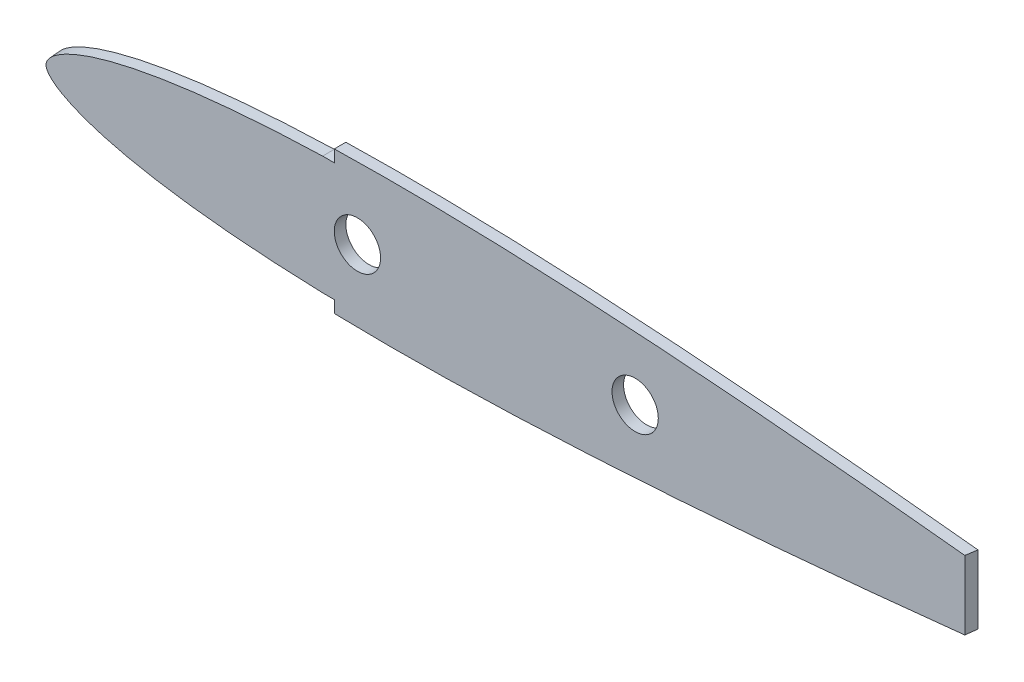
SolidWorks part; units mm, degrees
material "Balsa"
ref_plane "Front Plane" through (0, 0, 0) normal (0, 0, 1) x (1, 0, 0)
ref_plane "Top Plane" through (0, 0, 0) normal (0, 1, 0) x (1, 0, 0)
ref_plane "Right Plane" through (0, 0, 0) normal (1, 0, 0) x (0, 0, -1)
curve "Curve1"
  spline degree 3 poles (329.1277, -0.5559, 0) (329.1277, 0.5559, 0) (328.019, 0.4202, 0) (326.6142, 0.8156, 0) (324.0379, 1.0601, 0) (320.5673, 1.5846, 0) (316.0966, 2.17, 0) (310.7052, 2.8915, 0) (304.4072, 3.7071, 0) (297.2481, 4.6151, 0) (289.2699, 5.5996, 0) (280.5223, 6.6474, 0) (271.0592, 7.7455, 0) (260.9388, 8.8788, 0) (250.2237, 10.0335, 0) (238.9798, 11.1954, 0) (227.2766, 12.3494, 0) (215.1861, 13.4792, 0) (202.7829, 14.5702, 0) (190.1436, 15.604, 0) (177.3458, 16.5638, 0) (164.4685, 17.4317, 0) (151.5911, 18.1897, 0) (138.7929, 18.8185, 0) (126.1528, 19.3014, 0) (113.7486, 19.6226, 0) (101.6567, 19.7665, 0) (89.9516, 19.7217, 0) (78.7054, 19.4794, 0) (67.9873, 19.0335, 0) (57.8633, 18.3829, 0) (48.3955, 17.5295, 0) (39.6421, 16.48, 0) (31.6562, 15.2433, 0) (24.4863, 13.8323, 0) (18.1744, 12.263, 0) (12.7564, 10.5507, 0) (8.2599, 8.7113, 0) (4.699, 6.7573, 0) (2.0794, 4.6848, 0) (0.4016, 2.4437, 0) (-0.1872, 0, 0) (0.4016, -2.4437, 0) (2.0794, -4.6848, 0) (4.699, -6.7573, 0) (8.2599, -8.7113, 0) (12.7564, -10.5507, 0) (18.1744, -12.263, 0) (24.4863, -13.8323, 0) (31.6562, -15.2433, 0) (39.6421, -16.48, 0) (48.3955, -17.5295, 0) (57.8633, -18.3829, 0) (67.9873, -19.0335, 0) (78.7054, -19.4794, 0) (89.9516, -19.7217, 0) (101.6567, -19.7665, 0) (113.7486, -19.6226, 0) (126.1528, -19.3014, 0) (138.7929, -18.8185, 0) (151.5911, -18.1897, 0) (164.4685, -17.4317, 0) (177.3458, -16.5638, 0) (190.1436, -15.604, 0) (202.7829, -14.5702, 0) (215.1861, -13.4792, 0) (227.2766, -12.3494, 0) (238.9798, -11.1954, 0) (250.2237, -10.0335, 0) (260.9388, -8.8788, 0) (271.0592, -7.7455, 0) (280.5223, -6.6474, 0) (289.2699, -5.5996, 0) (297.2481, -4.6151, 0) (304.4072, -3.7071, 0) (310.7052, -2.8915, 0) (316.0966, -2.17, 0) (320.5673, -1.5846, 0) (324.0379, -1.0601, 0) (326.6142, -0.8156, 0) (328.019, -0.4202, 0) (329.1277, -0.5559, 0) (329.1277, 0.5559, 0) (328.019, 0.4202, 0) knots -0.004279 -0.001997 -0.001234 0 0.000762 0.003045 0.006832 0.012101 0.018818 0.026939 0.036415 0.047185 0.05918 0.072328 0.086544 0.101741 0.117823 0.134691 0.15224 0.170361 0.188941 0.207865 0.227016 0.246276 0.265525 0.284645 0.30352 0.322035 0.340078 0.357543 0.374325 0.39033 0.405464 0.419644 0.432793 0.444844 0.455738 0.465429 0.473886 0.481102 0.487102 0.491975 0.495931 0.499383 0.502835 0.50679 0.511664 0.517664 0.524879 0.533337 0.543028 0.553922 0.565972 0.579122 0.593302 0.608436 0.62444 0.641223 0.658687 0.676731 0.695245 0.714121 0.733241 0.75249 0.77175 0.7909 0.809825 0.828404 0.846525 0.864074 0.880942 0.897025 0.912222 0.926438 0.939585 0.951581 0.962351 0.971826 0.979948 0.986664 0.991933 0.995721 0.998003 0.998766 1 1.000762 1.003045 1.006832 periodic
sketch "Sketch1" plane through (0, 0, 0) normal (0, 0, 1) x (1, 0, 0)
  spline S0 degree 3 poles (329.1277, -0.5559) (329.1277, 0.5559) (328.019, 0.4202) (326.6142, 0.8156) (324.0379, 1.0601) (320.5673, 1.5846) (316.0966, 2.17) (310.7052, 2.8915) (304.4072, 3.7071) (297.2481, 4.6151) (289.2699, 5.5996) (280.5223, 6.6474) (271.0592, 7.7455) (260.9388, 8.8788) (250.2237, 10.0335) (238.9798, 11.1954) (227.2766, 12.3494) (215.1861, 13.4792) (202.7829, 14.5702) (190.1436, 15.604) (177.3458, 16.5638) (164.4685, 17.4317) (151.5911, 18.1897) (138.7929, 18.8185) (126.1528, 19.3014) (113.7486, 19.6226) (101.6567, 19.7665) (89.9516, 19.7217) (78.7054, 19.4794) (67.9873, 19.0335) (57.8633, 18.3829) (48.3955, 17.5295) (39.6421, 16.48) (31.6562, 15.2433) (24.4863, 13.8323) (18.1744, 12.263) (12.7564, 10.5507) (8.2599, 8.7113) (4.699, 6.7573) (2.0794, 4.6848) (0.4016, 2.4437) (-0.1872, 0) (0.4016, -2.4437) (2.0794, -4.6848) (4.699, -6.7573) (8.2599, -8.7113) (12.7564, -10.5507) (18.1744, -12.263) (24.4863, -13.8323) (31.6562, -15.2433) (39.6421, -16.48) (48.3955, -17.5295) (57.8633, -18.3829) (67.9873, -19.0335) (78.7054, -19.4794) (89.9516, -19.7217) (101.6567, -19.7665) (113.7486, -19.6226) (126.1528, -19.3014) (138.7929, -18.8185) (151.5911, -18.1897) (164.4685, -17.4317) (177.3458, -16.5638) (190.1436, -15.604) (202.7829, -14.5702) (215.1861, -13.4792) (227.2766, -12.3494) (238.9798, -11.1954) (250.2237, -10.0335) (260.9388, -8.8788) (271.0592, -7.7455) (280.5223, -6.6474) (289.2699, -5.5996) (297.2481, -4.6151) (304.4072, -3.7071) (310.7052, -2.8915) (316.0966, -2.17) (320.5673, -1.5846) (324.0379, -1.0601) (326.6142, -0.8156) (328.019, -0.4202) (329.1277, -0.5559) (329.1277, 0.5559) (328.019, 0.4202) knots -0.004279 -0.001997 -0.001234 0 0.000762 0.003045 0.006832 0.012101 0.018818 0.026939 0.036415 0.047185 0.05918 0.072328 0.086544 0.101741 0.117823 0.134691 0.15224 0.170361 0.188941 0.207865 0.227016 0.246276 0.265525 0.284645 0.30352 0.322035 0.340078 0.357543 0.374325 0.39033 0.405464 0.419644 0.432793 0.444844 0.455738 0.465429 0.473886 0.481102 0.487102 0.491975 0.495931 0.499383 0.502835 0.50679 0.511664 0.517664 0.524879 0.533337 0.543028 0.553922 0.565972 0.579122 0.593302 0.608436 0.62444 0.641223 0.658687 0.676731 0.695245 0.714121 0.733241 0.75249 0.77175 0.7909 0.809825 0.828404 0.846525 0.864074 0.880942 0.897025 0.912222 0.926438 0.939585 0.951581 0.962351 0.971826 0.979948 0.986664 0.991933 0.995721 0.998003 0.998766 1 1.000762 1.003045 1.006832 only from (328.93, 0.4145) to (328.93, 0.4145) construction
  spline S1 degree 3 poles (329.1277, -0.5559) (329.1277, 0.5559) (328.019, 0.4202) (326.6142, 0.8156) (324.0379, 1.0601) (320.5673, 1.5846) (316.0966, 2.17) (310.7052, 2.8915) (304.4072, 3.7071) (297.2481, 4.6151) (289.2699, 5.5996) (280.5223, 6.6474) (271.0592, 7.7455) (260.9388, 8.8788) (250.2237, 10.0335) (238.9798, 11.1954) (227.2766, 12.3494) (215.1861, 13.4792) (202.7829, 14.5702) (190.1436, 15.604) (177.3458, 16.5638) (164.4685, 17.4317) (151.5911, 18.1897) (138.7929, 18.8185) (126.1528, 19.3014) (113.7486, 19.6226) (101.6567, 19.7665) (89.9516, 19.7217) (78.7054, 19.4794) (67.9873, 19.0335) (57.8633, 18.3829) (48.3955, 17.5295) (39.6421, 16.48) (31.6562, 15.2433) (24.4863, 13.8323) (18.1744, 12.263) (12.7564, 10.5507) (8.2599, 8.7113) (4.699, 6.7573) (2.0794, 4.6848) (0.4016, 2.4437) (-0.1872, 0) (0.4016, -2.4437) (2.0794, -4.6848) (4.699, -6.7573) (8.2599, -8.7113) (12.7564, -10.5507) (18.1744, -12.263) (24.4863, -13.8323) (31.6562, -15.2433) (39.6421, -16.48) (48.3955, -17.5295) (57.8633, -18.3829) (67.9873, -19.0335) (78.7054, -19.4794) (89.9516, -19.7217) (101.6567, -19.7665) (113.7486, -19.6226) (126.1528, -19.3014) (138.7929, -18.8185) (151.5911, -18.1897) (164.4685, -17.4317) (177.3458, -16.5638) (190.1436, -15.604) (202.7829, -14.5702) (215.1861, -13.4792) (227.2766, -12.3494) (238.9798, -11.1954) (250.2237, -10.0335) (260.9388, -8.8788) (271.0592, -7.7455) (280.5223, -6.6474) (289.2699, -5.5996) (297.2481, -4.6151) (304.4072, -3.7071) (310.7052, -2.8915) (316.0966, -2.17) (320.5673, -1.5846) (324.0379, -1.0601) (326.6142, -0.8156) (328.019, -0.4202) (329.1277, -0.5559) (329.1277, 0.5559) (328.019, 0.4202) knots -0.004279 -0.001997 -0.001234 0 0.000762 0.003045 0.006832 0.012101 0.018818 0.026939 0.036415 0.047185 0.05918 0.072328 0.086544 0.101741 0.117823 0.134691 0.15224 0.170361 0.188941 0.207865 0.227016 0.246276 0.265525 0.284645 0.30352 0.322035 0.340078 0.357543 0.374325 0.39033 0.405464 0.419644 0.432793 0.444844 0.455738 0.465429 0.473886 0.481102 0.487102 0.491975 0.495931 0.499383 0.502835 0.50679 0.511664 0.517664 0.524879 0.533337 0.543028 0.553922 0.565972 0.579122 0.593302 0.608436 0.62444 0.641223 0.658687 0.676731 0.695245 0.714121 0.733241 0.75249 0.77175 0.7909 0.809825 0.828404 0.846525 0.864074 0.880942 0.897025 0.912222 0.926438 0.939585 0.951581 0.962351 0.971826 0.979948 0.986664 0.991933 0.995721 0.998003 0.998766 1 1.000762 1.003045 1.006832 only from (328.93, 0.4145) to (328.93, 0.4145)
extrude "Boss-Extrude1" add sketch "Sketch1" along normal blind 3.175
sketch "Sketch2" plane through (0, 0, 3.175) normal (0, 0, 1) x (1, 0, 0)
  circle A0 centre (88.9, 0) radius 6.35
  circle A1 centre (165.1, 0) radius 6.35
  dimension "D1" = 12.7
  dimension "D2" = 12.7
  dimension "D3" = 0
  dimension "D4" = 0
  dimension "D5" = 88.9
  dimension "D6" = 165.1
extrude "Cut-Extrude1" cut sketch "Sketch2" against normal through all
sketch "Sketch3" plane through (0, 0, 0) normal (0, 1, 0) x (1, 0, 0)
  line L2 (255.9922, 0) -> (255.5456, -3.175)
  line L4 (0, 0) -> (329.0783, 0) construction
  line L5 (255.9922, 0) -> (329.0783, 0)
  line L6 (0, -3.175) -> (329.0783, -3.175) construction
  line L7 (255.5456, -3.175) -> (329.0783, -3.175)
  line L8 (329.0783, -3.175) -> (329.0783, 0) construction
  line L9 (329.0783, -3.175) -> (329.0783, 0)
extrude "Cut-Extrude2" cut sketch "Sketch3" against normal through all both and the other way through all
sketch "Sketch4" plane through (0, 0, 3.175) normal (0, 0, 1) x (1, 0, 0)
  line L0 (82.55, -19.5157) -> (82.55, -16.251)
  line L1 (82.55, -19.5157) -> (82.55, -16.251)
  line L2 (82.55, 16.251) -> (82.55, 19.5157)
  line L3 (82.55, 16.251) -> (82.55, 19.5157)
  line L4 (79.375, 16.251) -> (82.55, 16.251)
  line L5 (79.375, 16.251) -> (82.55, 16.251)
  line L6 (82.55, -16.251) -> (79.375, -16.251)
  line L7 (82.55, -16.251) -> (79.375, -16.251)
  line L9 (0.5415, 30.0212) -> (-2.1465, -32.8507)
  line L11 (82.55, -19.5157) -> (82.55, -25.5256)
  line L12 (82.55, -25.5256) -> (-2.1465, -32.8507)
  line L13 (82.55, 19.5157) -> (82.55, 26.8567)
  line L14 (82.55, 26.8567) -> (0.5415, 30.0212)
  spline S0 degree 3 poles (633.1488, 1884.3857) (572.2625, -178.71) (305.5166, 33.3533) (56.3074, 15.0016) (53.0215, 14.7179) (46.4592, 14.0473) (43.1826, 13.6609) (38.2769, 12.9805) (36.6432, 12.7368) (33.3795, 12.2092) (31.7481, 11.9252) (28.4987, 11.3107) (26.8806, 10.9799) (23.6603, 10.2608) (22.0581, 9.8726) (18.8752, 9.0193) (17.294, 8.5555) (14.1628, 7.5173) (12.612, 6.9461) (10.325, 5.9501) (9.5678, 5.594) (8.4619, 5.0175) (8.0979, 4.8178) (7.3817, 4.3992) (7.0294, 4.1804) (6.3393, 3.7196) (6.0012, 3.478) (5.3468, 2.9597) (5.0286, 2.6811) (4.4393, 2.0844) (4.1647, 1.7684) (3.8202, 1.2362) (3.7187, 1.0506) (3.6, 0.7593) (3.5654, 0.6591) (3.5092, 0.4554) (3.4875, 0.3518) (3.4597, 0.1436) (3.4536, 0.0389) (3.4614, -0.1718) (3.475, -0.2784) (3.5362, -0.5884) (3.6037, -0.7864) (3.7802, -1.1687) (3.8895, -1.352) (4.1294, -1.699) (4.2613, -1.865) (4.6778, -2.343) (4.9796, -2.6343) (5.6143, -3.1819) (5.9478, -3.4375) (6.9802, -4.1679) (7.6955, -4.5988) (9.1563, -5.3913) (9.9024, -5.7532) (11.4148, -6.4327) (12.1816, -6.7494) (13.7316, -7.3466) (14.5148, -7.6272) (16.0932, -8.162) (16.8886, -8.4152) (18.4829, -8.8963) (19.2828, -9.1247) (21.6889, -9.78) (23.302, -10.1762) (26.5415, -10.9085) (28.1678, -11.2447) (33.063, -12.1804) (36.3505, -12.7096) (42.9384, -13.6309) (46.2381, -14.0227) (52.8462, -14.7022) (56.1547, -14.9893) (304.7791, -33.3808) (568.8134, 178.1804) (647.8146, -1880.4778) knots -4.547287 -4.547287 -4.547287 -4.547287 0.125 0.125 0.1875 0.1875 0.25 0.25 0.28125 0.28125 0.3125 0.3125 0.34375 0.34375 0.375 0.375 0.40625 0.40625 0.4375 0.4375 0.453125 0.453125 0.460938 0.460938 0.46875 0.46875 0.476563 0.476563 0.484375 0.484375 0.492188 0.492188 0.496094 0.496094 0.498047 0.498047 0.5 0.5 0.501953 0.501953 0.503906 0.503906 0.507813 0.507813 0.511719 0.511719 0.515625 0.515625 0.523438 0.523438 0.53125 0.53125 0.546875 0.546875 0.5625 0.5625 0.578125 0.578125 0.59375 0.59375 0.609375 0.609375 0.625 0.625 0.65625 0.65625 0.6875 0.6875 0.75 0.75 0.8125 0.8125 0.875 0.875 5.504372 5.504372 5.504372 5.504372 only from (79.375, 16.251) to (79.375, -16.251)
  spline S1 degree 3 poles (79.375, 16.251) (72.7703, 16.048) (66.1762, 15.7283) (56.3074, 15.0016) (53.0215, 14.7179) (46.4592, 14.0473) (43.1826, 13.6609) (38.2769, 12.9805) (36.6432, 12.7368) (33.3795, 12.2092) (31.7481, 11.9252) (28.4987, 11.3107) (26.8806, 10.9799) (23.6603, 10.2608) (22.0581, 9.8726) (18.8752, 9.0193) (17.294, 8.5555) (14.1628, 7.5173) (12.612, 6.9461) (10.325, 5.9501) (9.5678, 5.594) (8.4619, 5.0175) (8.0979, 4.8178) (7.3817, 4.3992) (7.0294, 4.1804) (6.3393, 3.7196) (6.0012, 3.478) (5.3468, 2.9597) (5.0286, 2.6811) (4.4393, 2.0844) (4.1647, 1.7684) (3.8202, 1.2362) (3.7187, 1.0506) (3.6, 0.7593) (3.5654, 0.6591) (3.5092, 0.4554) (3.4875, 0.3518) (3.4597, 0.1436) (3.4536, 0.0389) (3.4614, -0.1718) (3.475, -0.2784) (3.5362, -0.5884) (3.6037, -0.7864) (3.7802, -1.1687) (3.8895, -1.352) (4.1294, -1.699) (4.2613, -1.865) (4.6778, -2.343) (4.9796, -2.6343) (5.6143, -3.1819) (5.9478, -3.4375) (6.9802, -4.1679) (7.6955, -4.5988) (9.1563, -5.3913) (9.9024, -5.7532) (11.4148, -6.4327) (12.1816, -6.7494) (13.7316, -7.3466) (14.5148, -7.6272) (16.0932, -8.162) (16.8886, -8.4152) (18.4829, -8.8963) (19.2828, -9.1247) (21.6889, -9.78) (23.302, -10.1762) (26.5415, -10.9085) (28.1678, -11.2447) (33.063, -12.1804) (36.3505, -12.7096) (42.9384, -13.6309) (46.2381, -14.0227) (52.8462, -14.7022) (56.1547, -14.9893) (66.0905, -15.7243) (72.7279, -16.0468) (79.375, -16.251) knots 0 0 0 0 0.125 0.125 0.1875 0.1875 0.25 0.25 0.28125 0.28125 0.3125 0.3125 0.34375 0.34375 0.375 0.375 0.40625 0.40625 0.4375 0.4375 0.453125 0.453125 0.460938 0.460938 0.46875 0.46875 0.476563 0.476563 0.484375 0.484375 0.492188 0.492188 0.496094 0.496094 0.498047 0.498047 0.5 0.5 0.501953 0.501953 0.503906 0.503906 0.507813 0.507813 0.511719 0.511719 0.515625 0.515625 0.523438 0.523438 0.53125 0.53125 0.546875 0.546875 0.5625 0.5625 0.578125 0.578125 0.59375 0.59375 0.609375 0.609375 0.625 0.625 0.65625 0.65625 0.6875 0.6875 0.75 0.75 0.8125 0.8125 0.875 0.875 1 1 1 1
sketch "Sketch5" plane through (0, 0, 0) normal (0, 0, -1) x (-1, 0, 0)
  line L0 (-82.55, 16.2869) -> (-82.55, 19.5505)
  line L1 (-82.55, 16.2869) -> (-82.55, 19.5505)
  line L2 (-82.55, -16.2869) -> (-79.375, -16.2868)
  line L3 (-82.55, -16.2869) -> (-79.375, -16.2868)
  line L4 (-82.55, -19.5505) -> (-82.55, -16.2869)
  line L5 (-82.55, -19.5505) -> (-82.55, -16.2869)
  line L6 (-79.375, 16.2868) -> (-82.55, 16.2869)
  line L7 (-79.375, 16.2868) -> (-82.55, 16.2869)
  line L9 (6.7812, 29.8614) -> (6.7812, -36.6391)
  line L11 (-82.55, -19.5505) -> (-82.55, -25.5256)
  line L12 (-82.55, -25.5256) -> (6.7812, -36.6391)
  line L13 (-82.55, 19.5505) -> (-82.55, 31.3589)
  line L15 (6.7812, 29.8614) -> (-82.55, 31.3589)
  spline S0 degree 3 poles (-649.3041, -1879.8024) (-570.0365, 178.4573) (-305.3204, -33.3955) (-56.0669, -15.0268) (-52.7459, -14.7395) (-46.1126, -14.0593) (-42.8003, -13.6669) (-36.1868, -12.7438) (-32.8863, -12.2135) (-27.9721, -11.2755) (-26.3395, -10.9383) (-23.0875, -10.204) (-21.4682, -9.8067) (-19.0528, -9.1496) (-18.2498, -8.9205) (-16.6494, -8.4378) (-15.851, -8.1838) (-13.4745, -7.3791) (-11.9142, -6.7899) (-9.6372, -5.7671) (-8.8884, -5.4038) (-7.4222, -4.6083) (-6.7042, -4.1757) (-5.6681, -3.4422) (-5.3336, -3.1854) (-4.697, -2.6353) (-4.3942, -2.3426) (-3.9768, -1.8622) (-3.8446, -1.6954) (-3.6045, -1.3465) (-3.4952, -1.1622) (-3.3192, -0.7778) (-3.2523, -0.5788) (-3.1923, -0.2672) (-3.1792, -0.16) (-3.1725, 0.0517) (-3.1793, 0.1568) (-3.2233, 0.4702) (-3.2839, 0.6772) (-3.4449, 1.0664) (-3.5476, 1.2523) (-3.8954, 1.7853) (-4.1717, 2.1017) (-4.7642, 2.6996) (-5.084, 2.9787) (-5.7415, 3.4979) (-6.081, 3.74) (-7.1204, 4.4324) (-7.842, 4.8477) (-9.3223, 5.618) (-10.0826, 5.9749) (-12.3785, 6.9731) (-13.9351, 7.5453) (-17.0774, 8.5855) (-18.6641, 9.05) (-21.8582, 9.9049) (-23.466, 10.2937) (-26.6977, 11.014) (-28.3216, 11.3453) (-31.5826, 11.9608) (-33.2197, 12.2452) (-36.4949, 12.7735) (-38.1343, 13.0174) (-43.0571, 13.6986) (-46.345, 14.0853) (-52.9302, 14.7561) (-56.2275, 15.0397) (-306.0585, 33.3625) (-573.4075, -178.961) (-635.2065, 1883.5473) knots -4.498533 -4.498533 -4.498533 -4.498533 0.125 0.125 0.1875 0.1875 0.25 0.25 0.3125 0.3125 0.34375 0.34375 0.375 0.375 0.390625 0.390625 0.40625 0.40625 0.4375 0.4375 0.453125 0.453125 0.46875 0.46875 0.476563 0.476563 0.484375 0.484375 0.488281 0.488281 0.492188 0.492188 0.496094 0.496094 0.498047 0.498047 0.5 0.5 0.503906 0.503906 0.507813 0.507813 0.515625 0.515625 0.523438 0.523438 0.53125 0.53125 0.546875 0.546875 0.5625 0.5625 0.59375 0.59375 0.625 0.625 0.65625 0.65625 0.6875 0.6875 0.71875 0.71875 0.75 0.75 0.8125 0.8125 0.875 0.875 5.542695 5.542695 5.542695 5.542695 only from (-79.375, -16.2868) to (-79.375, 16.2868)
  spline S1 degree 3 poles (-79.375, -16.2868) (-72.7027, -16.0836) (-66.0402, -15.7617) (-56.0669, -15.0268) (-52.7459, -14.7395) (-46.1126, -14.0593) (-42.8003, -13.6669) (-36.1868, -12.7438) (-32.8863, -12.2135) (-27.9721, -11.2755) (-26.3395, -10.9383) (-23.0875, -10.204) (-21.4682, -9.8067) (-19.0528, -9.1496) (-18.2498, -8.9205) (-16.6494, -8.4378) (-15.851, -8.1838) (-13.4745, -7.3791) (-11.9142, -6.7899) (-9.6372, -5.7671) (-8.8884, -5.4038) (-7.4222, -4.6083) (-6.7042, -4.1757) (-5.6681, -3.4422) (-5.3336, -3.1854) (-4.697, -2.6353) (-4.3942, -2.3426) (-3.9768, -1.8622) (-3.8446, -1.6954) (-3.6045, -1.3465) (-3.4952, -1.1622) (-3.3192, -0.7778) (-3.2523, -0.5788) (-3.1923, -0.2672) (-3.1792, -0.16) (-3.1725, 0.0517) (-3.1793, 0.1568) (-3.2233, 0.4702) (-3.2839, 0.6772) (-3.4449, 1.0664) (-3.5476, 1.2523) (-3.8954, 1.7853) (-4.1717, 2.1017) (-4.7642, 2.6996) (-5.084, 2.9787) (-5.7415, 3.4979) (-6.081, 3.74) (-7.1204, 4.4324) (-7.842, 4.8477) (-9.3223, 5.618) (-10.0826, 5.9749) (-12.3785, 6.9731) (-13.9351, 7.5453) (-17.0774, 8.5855) (-18.6641, 9.05) (-21.8582, 9.9049) (-23.466, 10.2937) (-26.6977, 11.014) (-28.3216, 11.3453) (-31.5826, 11.9608) (-33.2197, 12.2452) (-36.4949, 12.7735) (-38.1343, 13.0174) (-43.0571, 13.6986) (-46.345, 14.0853) (-52.9302, 14.7561) (-56.2275, 15.0397) (-66.1305, 15.766) (-72.7475, 16.085) (-79.375, 16.2868) knots 0 0 0 0 0.125 0.125 0.1875 0.1875 0.25 0.25 0.3125 0.3125 0.34375 0.34375 0.375 0.375 0.390625 0.390625 0.40625 0.40625 0.4375 0.4375 0.453125 0.453125 0.46875 0.46875 0.476563 0.476563 0.484375 0.484375 0.488281 0.488281 0.492188 0.492188 0.496094 0.496094 0.498047 0.498047 0.5 0.5 0.503906 0.503906 0.507813 0.507813 0.515625 0.515625 0.523438 0.523438 0.53125 0.53125 0.546875 0.546875 0.5625 0.5625 0.59375 0.59375 0.625 0.625 0.65625 0.65625 0.6875 0.6875 0.71875 0.71875 0.75 0.75 0.8125 0.8125 0.875 0.875 1 1 1 1
loft "Cut-Loft1" cut profiles "Sketch4", "Sketch5"
